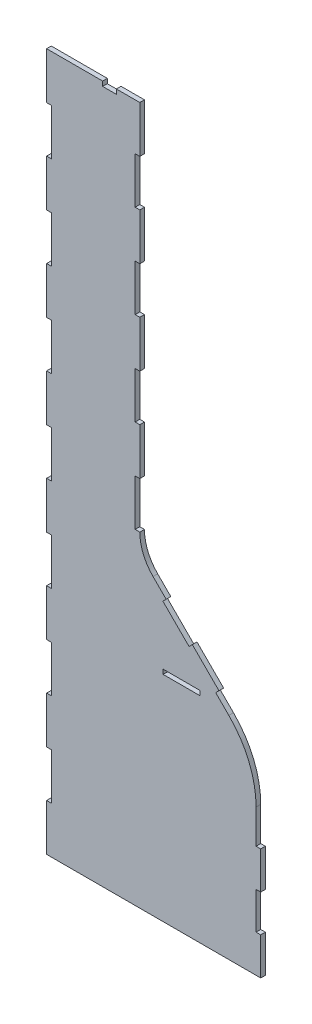
SolidWorks part; units mm, degrees
material "Contreplaqué pin"
ref_plane "Plan de face" through (0, 0, 0) normal (0, 0, 1) x (1, 0, 0)
ref_plane "Plan de dessus" through (0, 0, 0) normal (0, 1, 0) x (1, 0, 0)
ref_plane "Plan de droite" through (0, 0, 0) normal (1, 0, 0) x (0, 0, -1)
sketch "Esquisse1" plane through (0, 0, 0) normal (0, 0, 1) x (1, 0, 0)
  line L0 (100, 330) -> (128.2843, 301.7157) construction
  line L2 (0, 0) -> (0, 50) construction
  line L3 (0, 750) -> (60, 750) construction
  line L4 (100, 330) -> (100, 350) construction
  line L5 (230, 200) -> (230, 160) construction
  line L6 (230, 0) -> (0, 0) construction
  line L12 (0, 100) -> (0, 150) construction
  line L13 (0, 600) -> (5, 600) construction
  line L15 (0, 550) -> (5, 550) construction
  line L16 (5, 600) -> (5, 550) construction
  line L17 (0, 500) -> (5, 500) construction
  line L19 (0, 450) -> (5, 450) construction
  line L20 (5, 500) -> (5, 450) construction
  line L21 (0, 300) -> (5, 300) construction
  line L23 (0, 250) -> (5, 250) construction
  line L24 (5, 300) -> (5, 250) construction
  line L25 (0, 100) -> (5, 100) construction
  line L27 (0, 50) -> (5, 50) construction
  line L28 (5, 100) -> (5, 50) construction
  line L29 (0, 400) -> (5, 400) construction
  line L31 (0, 350) -> (5, 350) construction
  line L32 (5, 400) -> (5, 350) construction
  line L33 (0, 200) -> (5, 200) construction
  line L35 (0, 150) -> (5, 150) construction
  line L36 (5, 200) -> (5, 150) construction
  line L37 (0, 200) -> (0, 250) construction
  line L38 (0, 300) -> (0, 350) construction
  line L39 (0, 400) -> (0, 450) construction
  line L40 (0, 500) -> (0, 550) construction
  line L41 (0, 600) -> (0, 650) construction
  line L42 (0, 700) -> (0, 750) construction
  line L43 (0, 650) -> (5, 650) construction
  line L45 (0, 700) -> (5, 700) construction
  line L46 (5, 650) -> (5, 700) construction
  line L47 (100, 700) -> (100, 750) construction
  line L48 (100, 700) -> (95, 700) construction
  line L50 (100, 650) -> (95, 650) construction
  line L51 (95, 700) -> (95, 650) construction
  line L52 (100, 600) -> (95, 600) construction
  line L54 (100, 550) -> (95, 550) construction
  line L55 (95, 600) -> (95, 550) construction
  line L56 (100, 500) -> (95, 500) construction
  line L58 (100, 450) -> (95, 450) construction
  line L59 (95, 500) -> (95, 450) construction
  line L60 (100, 400) -> (95, 400) construction
  line L62 (100, 350) -> (95, 350) construction
  line L63 (95, 400) -> (95, 350) construction
  line L64 (100, 600) -> (100, 650) construction
  line L65 (100, 500) -> (100, 550) construction
  line L66 (100, 400) -> (100, 450) construction
  line L67 (128.2843, 301.7157) -> (124.7487, 298.1802) construction
  line L68 (124.7487, 298.1802) -> (153.033, 269.8959) construction
  line L69 (153.033, 269.8959) -> (156.5685, 273.4315) construction
  line L70 (156.5685, 273.4315) -> (199.9019, 230.0981) construction
  line L71 (214.9509, 215.0491) -> (211.4154, 211.5135) construction
  line L72 (211.4154, 211.5135) -> (196.3663, 226.5626) construction
  line L73 (196.3663, 226.5626) -> (199.9019, 230.0981) construction
  line L74 (214.9509, 215.0491) -> (230, 200) construction
  line L75 (184.8528, 245.1472) -> (169.337, 229.6314) construction
  line L76 (230, 120) -> (230, 80) construction
  line L77 (230, 40) -> (225, 40) construction
  line L79 (230, 80) -> (225, 80) construction
  line L80 (225, 40) -> (225, 80) construction
  line L81 (230, 120) -> (225, 120) construction
  line L83 (230, 160) -> (225, 160) construction
  line L84 (225, 120) -> (225, 160) construction
  line L85 (230, 40) -> (230, 0) construction
  line L87 (125, 235.1) -> (165, 235.1) construction
  line L88 (125, 235.1) -> (125, 230) construction
  line L89 (125, 230) -> (165, 230) construction
  line L90 (165, 235.1) -> (165, 230) construction
  line L94 (60, 750) -> (60, 745) construction
  line L95 (60, 745) -> (75, 745) construction
  line L96 (75, 745) -> (75, 750) construction
  line L97 (75, 750) -> (100, 750) construction
  line L98 (100.1, 330.0414) -> (128.4257, 301.7157)
  line L99 (128.4257, 301.7157) -> (124.8902, 298.1802)
  line L100 (124.8902, 298.1802) -> (153.033, 270.0373)
  line L101 (153.033, 270.0373) -> (156.5685, 273.5729)
  line L102 (156.5685, 273.5729) -> (200.0433, 230.0981)
  line L103 (196.5078, 226.5626) -> (200.0433, 230.0981)
  line L104 (211.4154, 211.6549) -> (196.5078, 226.5626)
  line L105 (214.9509, 215.1905) -> (211.4154, 211.6549)
  line L106 (214.9509, 215.1905) -> (230.1, 200.0414)
  line L107 (230.1, 200.0414) -> (230.1, 159.9)
  line L108 (230.1, 159.9) -> (225.1, 159.9)
  line L109 (225.1, 120.1) -> (225.1, 159.9)
  line L110 (230.1, 120.1) -> (225.1, 120.1)
  line L111 (230.1, 120.1) -> (230.1, 79.9)
  line L112 (230.1, 79.9) -> (225.1, 79.9)
  line L113 (225.1, 40.1) -> (225.1, 79.9)
  line L114 (230.1, 40.1) -> (225.1, 40.1)
  line L115 (230.1, 40.1) -> (230.1, -0.1)
  line L116 (230.1, -0.1) -> (-0.1, -0.1)
  line L117 (-0.1, -0.1) -> (-0.1, 50.1)
  line L118 (-0.1, 50.1) -> (4.9, 50.1)
  line L119 (4.9, 99.9) -> (4.9, 50.1)
  line L120 (-0.1, 99.9) -> (4.9, 99.9)
  line L121 (-0.1, 99.9) -> (-0.1, 150.1)
  line L122 (-0.1, 150.1) -> (4.9, 150.1)
  line L123 (4.9, 199.9) -> (4.9, 150.1)
  line L124 (-0.1, 199.9) -> (4.9, 199.9)
  line L125 (-0.1, 199.9) -> (-0.1, 250.1)
  line L126 (-0.1, 250.1) -> (4.9, 250.1)
  line L127 (4.9, 299.9) -> (4.9, 250.1)
  line L128 (-0.1, 299.9) -> (4.9, 299.9)
  line L129 (-0.1, 299.9) -> (-0.1, 350.1)
  line L130 (-0.1, 350.1) -> (4.9, 350.1)
  line L131 (4.9, 399.9) -> (4.9, 350.1)
  line L132 (-0.1, 399.9) -> (4.9, 399.9)
  line L133 (-0.1, 399.9) -> (-0.1, 450.1)
  line L134 (-0.1, 450.1) -> (4.9, 450.1)
  line L135 (4.9, 499.9) -> (4.9, 450.1)
  line L136 (-0.1, 499.9) -> (4.9, 499.9)
  line L137 (-0.1, 499.9) -> (-0.1, 550.1)
  line L138 (-0.1, 550.1) -> (4.9, 550.1)
  line L139 (4.9, 599.9) -> (4.9, 550.1)
  line L140 (-0.1, 599.9) -> (4.9, 599.9)
  line L141 (-0.1, 599.9) -> (-0.1, 650.1)
  line L142 (-0.1, 650.1) -> (4.9, 650.1)
  line L143 (4.9, 650.1) -> (4.9, 699.9)
  line L144 (-0.1, 699.9) -> (4.9, 699.9)
  line L145 (-0.1, 699.9) -> (-0.1, 750.1)
  line L146 (-0.1, 750.1) -> (60.1, 750.1)
  line L147 (60.1, 750.1) -> (60.1, 745.1)
  line L148 (60.1, 745.1) -> (74.9, 745.1)
  line L149 (74.9, 745.1) -> (74.9, 750.1)
  line L150 (74.9, 750.1) -> (100.1, 750.1)
  line L151 (100.1, 699.9) -> (100.1, 750.1)
  line L152 (100.1, 699.9) -> (95.1, 699.9)
  line L153 (95.1, 699.9) -> (95.1, 650.1)
  line L154 (100.1, 650.1) -> (95.1, 650.1)
  line L155 (100.1, 599.9) -> (100.1, 650.1)
  line L156 (100.1, 599.9) -> (95.1, 599.9)
  line L157 (95.1, 599.9) -> (95.1, 550.1)
  line L158 (100.1, 550.1) -> (95.1, 550.1)
  line L159 (100.1, 499.9) -> (100.1, 550.1)
  line L160 (100.1, 499.9) -> (95.1, 499.9)
  line L161 (95.1, 499.9) -> (95.1, 450.1)
  line L162 (100.1, 450.1) -> (95.1, 450.1)
  line L163 (100.1, 399.9) -> (100.1, 450.1)
  line L164 (100.1, 399.9) -> (95.1, 399.9)
  line L165 (95.1, 399.9) -> (95.1, 350.1)
  line L166 (100.1, 350.1) -> (95.1, 350.1)
  line L167 (100.1, 330.0414) -> (100.1, 350.1)
  line L168 (125.1, 235) -> (164.9, 235)
  line L169 (164.9, 235) -> (164.9, 230.1)
  line L170 (125.1, 230.1) -> (164.9, 230.1)
  line L171 (125.1, 235) -> (125.1, 230.1)
  dimension "D2" = 750
  dimension "D3" = 200
  dimension "D4" = 45
  dimension "D5" = 130
  dimension "D6" = 330
  dimension "D10" = 50
  dimension "D12" = 50
  dimension "D11" = 5
  dimension "D13" = 5
  dimension "D14" = 50
  dimension "D15" = 50
  dimension "D16" = 5
  dimension "D18" = 5
  dimension "D19" = 120
  dimension "D20" = 63.8478
  dimension "D21" = 21.2826
  dimension "D22" = 21.2826
  dimension "D17" = 40
  dimension "D23" = 40
  dimension "D24" = 5
  dimension "D26" = 5.1
  dimension "D27" = 25
  dimension "D28" = 40
  dimension "D29" = 100
  dimension "D25" = 40
  dimension "D7" = 60
  dimension "D9" = 100
  dimension "D8" = 15
  dimension "D30" = 5
  dimension "D31" = 0.1
  dimension "D32" = 0.1
extrude "Boss.-Extru.1" add sketch "Esquisse1" along normal blind 5
sketch "Esquisse3" plane through (0, 0, 5) normal (0, 0, 1) x (1, 0, 0)
  line L2 (200.0433, 230.0981) -> (156.5685, 273.5729) construction
  line L3 (211.4154, 211.6549) -> (196.5078, 226.5626) construction
  line L5 (225.1, 120.1) -> (225.1, 159.9) construction
  line L7 (230.1, 159.9) -> (230.1, 200.0414) construction
  line L10 (225.1, 156.549) -> (230.1, 156.549)
  line L11 (230.1, 156.549) -> (230.1, 200.0414)
  line L13 (195.8107, 227.2597) -> (181.6685, 241.4018)
  line L14 (181.6685, 241.4018) -> (185.2041, 244.9373)
  line L15 (185.2041, 244.9373) -> (230.1, 200.0414)
  arc A0 (225.1, 156.549) -> (195.8107, 227.2597) centre (125.1, 156.549) ccw
  point P5 (0, 0)
  point P17 (0, 0)
  dimension "D1" = 100
  dimension "D2" = 20
extrude "Enlèv. mat.-Extru.1" cut sketch "Esquisse3" against normal up to next
sketch "Esquisse4" plane through (0, 0, 5) normal (0, 0, 1) x (1, 0, 0)
  line L2 (100.1, 350.1) -> (100.1, 330.0414)
  line L3 (100.1, 330.0414) -> (114.2836, 315.8579)
  line L4 (100.1, 330.0414) -> (100.1, 350.1) construction
  line L5 (128.4257, 301.7157) -> (100.1, 330.0414) construction
  line L7 (100.1, 350.1) -> (95.1, 350.1) construction
  arc A0 (114.2836, 315.8579) -> (100.1, 350.1) centre (148.5257, 350.1) cw
  point P3 (0, 0)
  point P5 (0, 0)
  point P6 (0, 0)
  point P14 (0, 0)
extrude "Boss.-Extru.2" add sketch "Esquisse4" against normal blind 5
equation "\"D21@Esquisse1\"=\"D20@Esquisse1\"/3"
equation "\"D17@Esquisse1\"=\"D19@Esquisse1\"/3"
equation "\"D23@Esquisse1\"=\"D19@Esquisse1\"/3"
